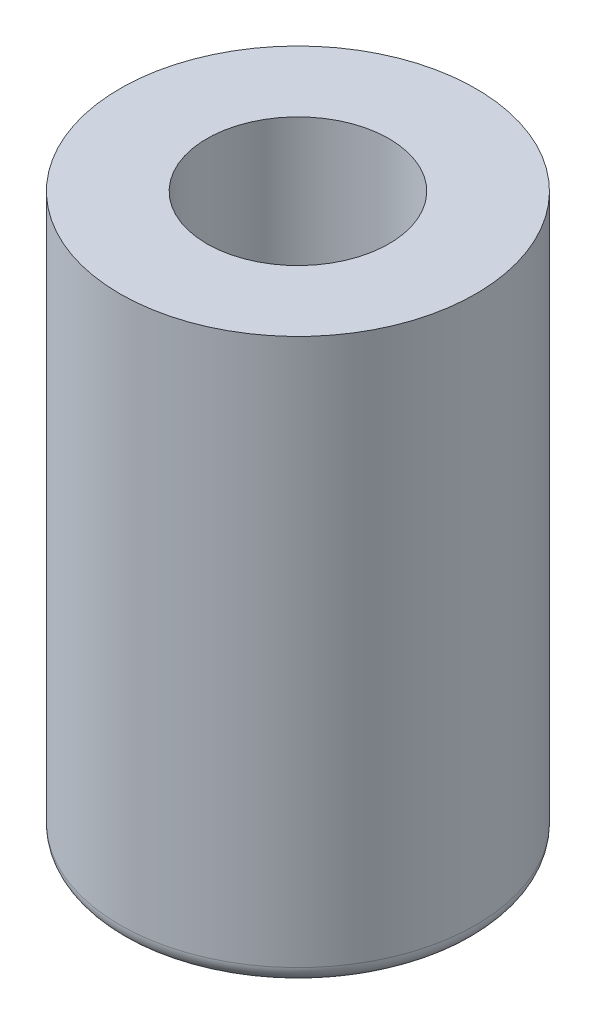
SolidWorks part; units mm, degrees
ref_plane "前视基准面" through (0, 0, 0) normal (0, 0, 1) x (1, 0, 0)
ref_plane "上视基准面" through (0, 0, 0) normal (0, 1, 0) x (1, 0, 0)
ref_plane "右视基准面" through (0, 0, 0) normal (1, 0, 0) x (0, 0, -1)
sketch "草图1" plane through (0, 0, 0) normal (0, 1, 0) x (1, 0, 0)
  circle A0 centre (0, 0) radius 1.05
  circle A1 centre (0, 0) radius 2.05
  dimension "D1" = 2.1
  dimension "D2" = 1
extrude "凸台-拉伸1" add sketch "草图1" along normal blind 7.5
fillet "圆角1" radius 0.2 4 edges at (0, 0, 1.05) (0, 0, 2.05) (0, 7.5, 1.05) (0, 7.5, 2.05)
sketch "草图2" plane through (0, 7.5, 0) normal (0, 1, 0) x (1, 0, 0)
  circle A0 centre (0, 0) radius 3.05
extrude "切除-拉伸1" cut sketch "草图2" against normal blind 1
